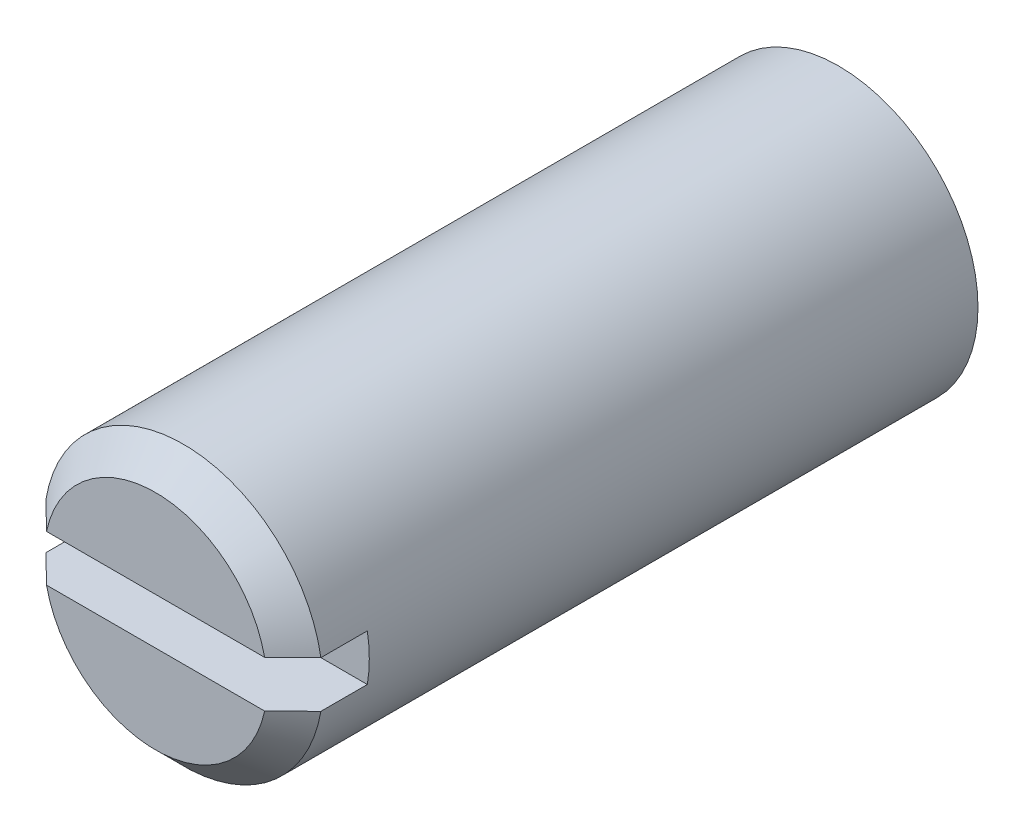
SolidWorks part; units mm, degrees
material "Простая углеродистая сталь"
ref_plane "Спереди" through (0, 0, 0) normal (0, 0, 1) x (1, 0, 0)
ref_plane "Сверху" through (0, 0, 0) normal (0, 1, 0) x (1, 0, 0)
ref_plane "Справа" through (0, 0, 0) normal (1, 0, 0) x (0, 0, -1)
sketch "Эскиз1" plane through (0, 0, 0) normal (0, 1, 0) x (1, 0, 0)
  line L0 (0, 0) -> (-3, 0)
  line L1 (-3, 0) -> (-3, 14.701)
  line L2 (-0.75, 16) -> (0, 16)
  line L3 (0, 16) -> (0, 0)
  line L4 (-0.75, 16) -> (-3, 14.701)
  dimension "D1" = 0.75
  dimension "D2" = 3
  dimension "D3" = 16
  dimension "D4" = 60
revolve "Повернуть1" add sketch "Эскиз1" angle 360 about L3
sketch "Эскиз2" plane through (0, 0, 0) normal (1, 0, 0) x (0, 0, -1)
  line L0 (0, 0) -> (50000, 0) construction
  line L1 (0, -0.5) -> (0, 0.5)
  line L2 (0, 3) -> (0, -3) construction
  line L3 (0, 0.5) -> (1.6, 0.5)
  line L4 (0, -0.5) -> (1.6, -0.5)
  line L5 (1.6, 0.5) -> (1.6, -0.5)
  point P8 (0, 0)
  point P10 (1.6, 0)
  dimension "D1" = 1
  dimension "D2" = 1.6
extrude "Вырез-Вытянуть1" cut sketch "Эскиз2" against normal through all both and the other way through all
chamfer "Фаска1" distance 0.6 angle 45 2 edges at (0, -3, 0) (0, 3, 0)
